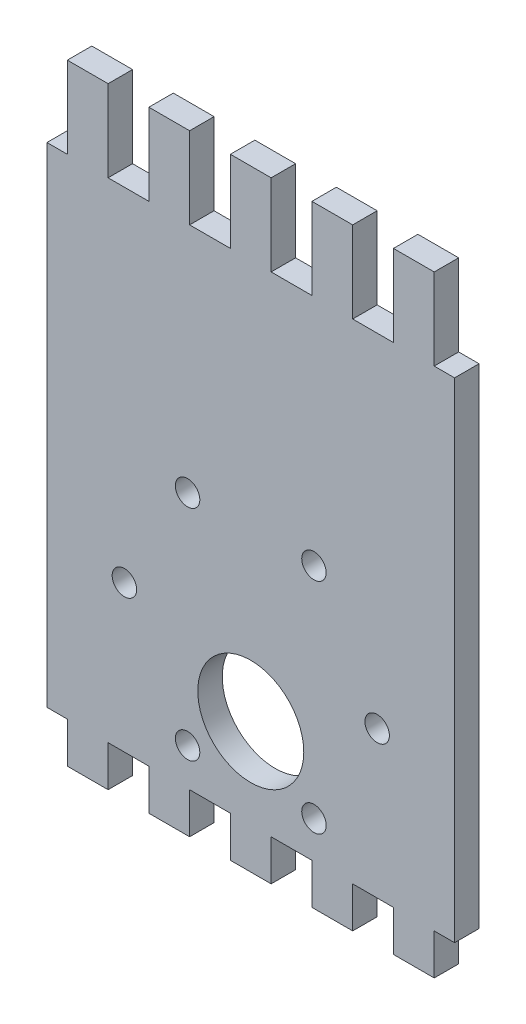
SolidWorks part; units mm, degrees
material "Balsa"
ref_plane "Plan de face" through (0, 0, 0) normal (0, 0, 1) x (1, 0, 0)
ref_plane "Plan de dessus" through (0, 0, 0) normal (0, 1, 0) x (1, 0, 0)
ref_plane "Plan de droite" through (0, 0, 0) normal (1, 0, 0) x (0, 0, -1)
sketch "Esquisse3" plane through (0, 0, 0) normal (0, 0, 1) x (1, 0, 0)
  line L0 (0, 70.5597) -> (0, -65.6935) construction
  line L2 (-25, 22) -> (25, 22)
  line L3 (-25, 22) -> (-25, -38)
  line L4 (-25, -38) -> (25, -38)
  line L5 (25, 22) -> (25, -38)
  dimension "D1" = 22
  dimension "D2" = 25
  dimension "D3" = 50
  dimension "D4" = 60
extrude "Boss.-Extru.12" add sketch "Esquisse3" along normal blind 3
sketch "Esquisse4" plane through (0, 0, 3) normal (0, 0, 1) x (1, 0, 0)
  line L0 (0, 0.0622) -> (0, -20) construction
  line L1 (0, -20) -> (-7.75, -6.5766) construction
  line L2 (-7.75, -33.4234) -> (0, -20) construction
  line L3 (0, -20) -> (-15.5, -20) construction
  line L4 (-25, -38) -> (25, -38) construction
  line L6 (-25, 22) -> (-25, -38) construction
  circle A0 centre (0, -20) radius 15.5 construction
  circle A1 centre (-7.75, -6.5766) radius 1.5
  circle A2 centre (-15.5, -20) radius 1.5
  circle A3 centre (-7.75, -33.4234) radius 1.5
  dimension "D1" = 31
  dimension "D4" = 3
  dimension "D5" = 3
  dimension "D6" = 3
  dimension "D3" = 30
  dimension "D7" = 60
  dimension "D8" = 60
  dimension "D9" = 18
  dimension "D10" = 25
extrude "Enlèv. mat.-Extru.1" cut sketch "Esquisse4" against normal blind 5
sketch "Esquisse6" plane through (0, 0, 3) normal (0, 0, 1) x (1, 0, 0)
  line L0 (-25, -38) -> (25, -38) construction
  line L2 (25, -38) -> (25, 22) construction
  circle A0 centre (0, -27) radius 6.5
  point P7 (25, -12.0305)
  point P8 (-48.1869, 3.2287)
  point P9 (-55.0704, 11.0673)
  dimension "D2" = 13
  dimension "D1" = 7
  dimension "D3" = 11
  dimension "D4" = 25
extrude "Enlèv. mat.-Extru.3" cut sketch "Esquisse6" against normal blind 10
mirror "Symétrie3" about plane through (0, 0, 0) normal (1, 0, 0) of "Enlèv. mat.-Extru.1"
sketch "Esquisse7" plane through (0, 0, 3) normal (0, 0, 1) x (1, 0, 0)
  line L0 (25, 22) -> (-25, 22) construction
  line L1 (-22.5, 22) -> (-17.5, 22)
  line L2 (-22.5, 22) -> (-22.5, 32)
  line L3 (-22.5, 32) -> (-17.5, 32)
  line L4 (-17.5, 22) -> (-17.5, 32)
  line L5 (-25, -38) -> (25, -38) construction
  line L6 (-22.5, -38) -> (-17.5, -38)
  line L7 (-22.5, -38) -> (-22.5, -43)
  line L8 (-22.5, -43) -> (-17.5, -43)
  line L9 (-17.5, -38) -> (-17.5, -43)
  line L10 (-25, 22) -> (-25, -38) construction
  dimension "D1" = 5
  dimension "D2" = 10
  dimension "D3" = 2.5
  dimension "D4" = 2.5
  dimension "D5" = 5
  dimension "D6" = 5
extrude "Boss.-Extru.13" add sketch "Esquisse7" against normal blind 3
pattern_linear "Répétition linéaire1" count 5 spacing 10 along (1, 0, 0) of "Boss.-Extru.13"
